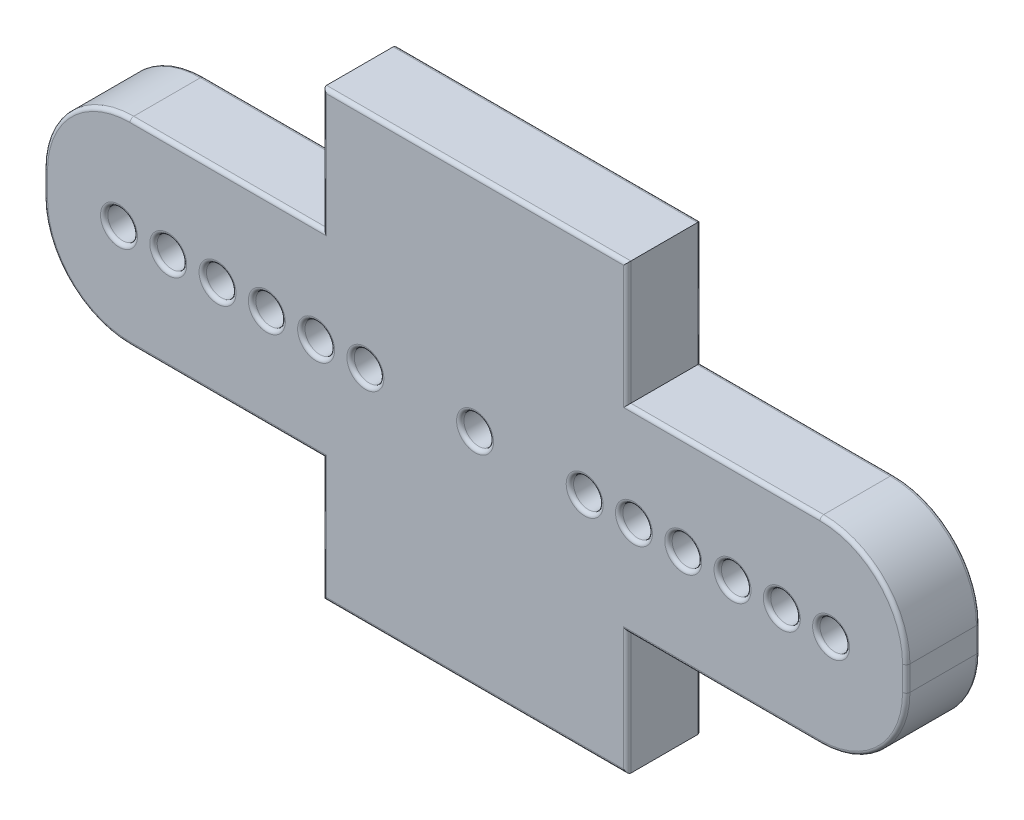
SolidWorks part; units mm, degrees
ref_plane "Płaszczyzna przednia" through (0, 0, 0) normal (0, 0, 1) x (1, 0, 0)
ref_plane "Płaszczyzna górna" through (0, 0, 0) normal (0, 1, 0) x (1, 0, 0)
ref_plane "Płaszczyzna prawa" through (0, 0, 0) normal (1, 0, 0) x (0, 0, -1)
sketch "Szkic1" plane through (0, 0, 0) normal (0, 0, 1) x (1, 0, 0)
  line L0 (-17.5, -0.5) -> (-17.5, 0.5)
  line L1 (-6.175, -9) -> (6.175, -9) construction
  line L2 (-6.175, -9) -> (-6.175, 9) construction
  line L3 (-6.175, 9) -> (6.175, 9) construction
  line L4 (6.175, -9) -> (6.175, 9) construction
  line L5 (-6.175, -9) -> (6.175, 9) construction
  line L6 (-6.175, 9) -> (6.175, -9) construction
  line L7 (-17.5, -4) -> (17.5, -4) construction
  line L8 (-17.5, -4) -> (-17.5, 4) construction
  line L9 (-17.5, 4) -> (17.5, 4) construction
  line L10 (17.5, -4) -> (17.5, 4) construction
  line L11 (-17.5, -4) -> (17.5, 4) construction
  line L12 (-17.5, 4) -> (17.5, -4) construction
  line L13 (-14, 4) -> (-6.175, 4)
  line L14 (-6.175, 4) -> (-6.175, 9)
  line L15 (-6.175, 9) -> (6.175, 9)
  line L16 (6.175, 9) -> (6.175, 4)
  line L17 (6.175, 4) -> (14, 4)
  line L18 (17.5, 0.5) -> (17.5, -0.5)
  line L19 (14, -4) -> (6.175, -4)
  line L20 (6.175, -4) -> (6.175, -9)
  line L21 (6.175, -9) -> (-6.175, -9)
  line L22 (-6.175, -9) -> (-6.175, -4)
  line L23 (-6.175, -4) -> (-14, -4)
  arc A0 (14, 4) -> (17.5, 0.5) centre (14, 0.5) cw
  arc A1 (17.5, -0.5) -> (14, -4) centre (14, -0.5) cw
  arc A2 (-14, 4) -> (-17.5, 0.5) centre (-14, 0.5) ccw
  arc A3 (-17.5, -0.5) -> (-14, -4) centre (-14, -0.5) ccw
  point P0 (0, 0)
  point P6 (0, 0)
  dimension "D5" = 3.5
  dimension "D1" = 8
  dimension "D2" = 35
  dimension "D3" = 18
  dimension "D4" = 12.35
extrude "Dodanie-wyciągnięcie1" add sketch "Szkic1" along normal mid plane 3
sketch "Szkic2" plane through (0, 0, 1.5) normal (0, 0, 1) x (1, 0, 0)
  line L1 (0, -9) -> (0, 9) construction
  line L2 (6.175, 9) -> (-6.175, 9) construction
  circle A0 centre (0, 0) radius 3.45 construction
  circle A13 centre (0, 0) radius 0.6
  point P22 (0, 0)
  dimension "D1" = 6.9
  dimension "D7" = 1.2
extrude "Wytnij-wyciągnięcie1" cut sketch "Szkic2" against normal through all
sketch "Szkic3" plane through (0, 0, 1.5) normal (0, 0, 1) x (1, 0, 0)
  line L0 (-4.45, 0) -> (-6.45, 0) construction
  circle A0 centre (-4.45, 0) radius 0.6
  circle A1 centre (-6.45, 0) radius 0.6
  circle A2 centre (-8.45, 0) radius 0.6
  circle A3 centre (-10.45, 0) radius 0.6
  circle A4 centre (-12.45, 0) radius 0.6
  circle A5 centre (-14.45, 0) radius 0.6
  dimension "D1" = 1.2
  dimension "D2" = 4.45
  dimension "D4" = 2
  dimension "D3" = 6
extrude "Wytnij-wyciągnięcie2" cut sketch "Szkic3" against normal through all
mirror "Lustro1" about plane through (0, 0, 0) normal (1, 0, 0) of "Wytnij-wyciągnięcie2"
fillet "Zaokrąglenie1" radius 0.15 58 edges at (0, 9, -1.5) (-6.175, 6.5, -1.5) (-10.0875, 4, -1.5) (-17.5, 0, -1.5) (-10.0875, -4, -1.5) (-6.175, -6.5, -1.5) (0, -9, -1.5) (6.175, -6.5, -1.5) (10.0875, -4, -1.5) (17.5, 0, -1.5) (10.0875, 4, -1.5) (6.175, 6.5, -1.5) (0.6, 0, -1.5) (-13.85, 0, -1.5) (-11.85, 0, -1.5) (-9.85, 0, -1.5) (-7.85, 0, -1.5) (-5.85, 0, -1.5) (-3.85, 0, -1.5) (13.85, 0, -1.5) (11.85, 0, -1.5) (9.85, 0, -1.5) (7.85, 0, -1.5) (5.85, 0, -1.5) (3.85, 0, -1.5) (10.0875, 4, 1.5) (17.5, 0, 1.5) (10.0875, -4, 1.5) (6.175, -6.5, 1.5) (0, -9, 1.5) (-6.175, -6.5, 1.5) (-10.0875, -4, 1.5) (-17.5, 0, 1.5) (-10.0875, 4, 1.5) (-6.175, 6.5, 1.5) (0, 9, 1.5) (6.175, 6.5, 1.5) (0.6, 0, 1.5) (-13.85, 0, 1.5) (-11.85, 0, 1.5) (-9.85, 0, 1.5) (-7.85, 0, 1.5) (-5.85, 0, 1.5) (-3.85, 0, 1.5) (13.85, 0, 1.5) (11.85, 0, 1.5) (9.85, 0, 1.5) (7.85, 0, 1.5) (5.85, 0, 1.5) (3.85, 0, 1.5) (-16.4749, 2.9749, -1.5) (-16.4749, -2.9749, -1.5) (16.4749, -2.9749, -1.5) (16.4749, 2.9749, -1.5) (16.4749, 2.9749, 1.5) (16.4749, -2.9749, 1.5) (-16.4749, -2.9749, 1.5) (-16.4749, 2.9749, 1.5)
